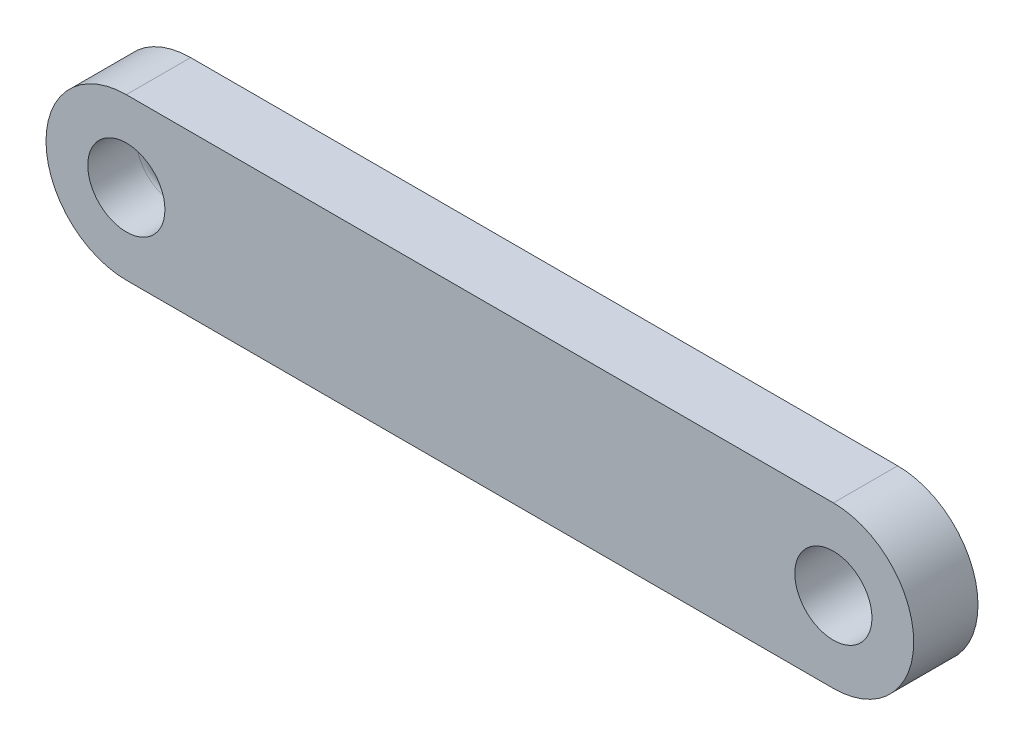
SolidWorks part; units mm, degrees
ref_plane "Front Plane" through (0, 0, 0) normal (0, 0, 1) x (1, 0, 0)
ref_plane "Top Plane" through (0, 0, 0) normal (0, 1, 0) x (1, 0, 0)
ref_plane "Right Plane" through (0, 0, 0) normal (1, 0, 0) x (0, 0, -1)
sketch "Sketch1" plane through (0, 0, 0) normal (0, 0, 1) x (1, 0, 0)
  line L2 (0, 25) -> (220, 25)
  line L3 (0, -25) -> (220, -25)
  arc A1 (0, 25) -> (0, -25) centre (0, 0) ccw
  arc A2 (220, -25) -> (220, 25) centre (220, 0) ccw
  circle A3 centre (220, 0) radius 12
  circle A4 centre (0, 0) radius 12
  dimension "D1" = 24
  dimension "D3" = 50
  dimension "D5" = 24
  dimension "D4" = 220
extrude "Boss-Extrude1" add sketch "Sketch1" along normal blind 20
fillet "Fillet1" radius 5 1 edges at (12, 0, 0)
